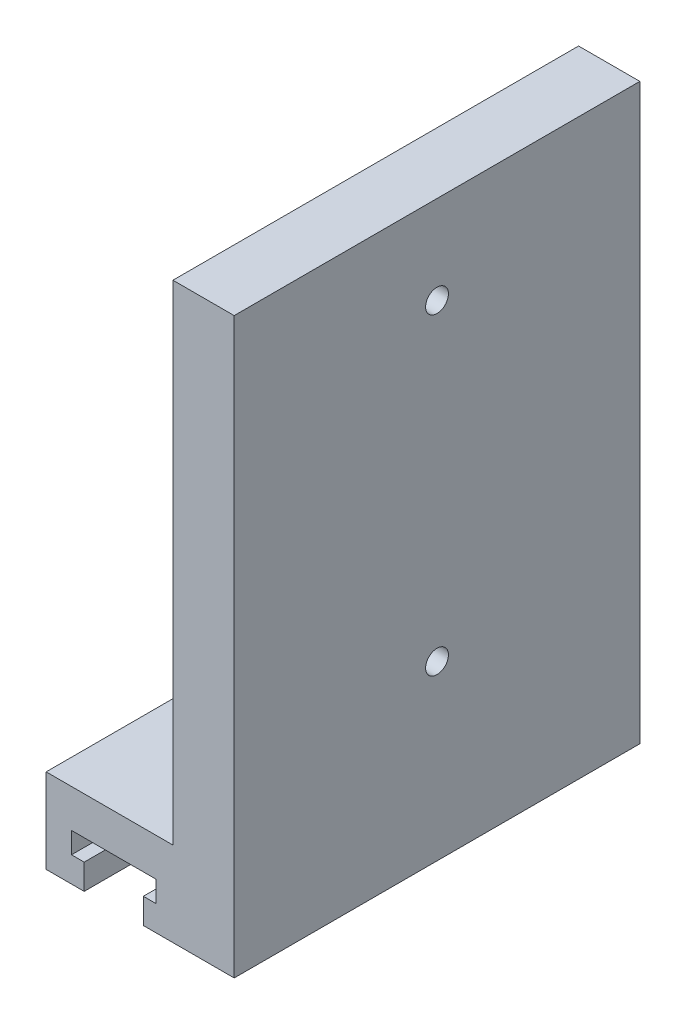
SolidWorks part; units mm, degrees
material "ABS"
ref_plane "Front Plane" through (0, 0, 0) normal (0, 0, 1) x (1, 0, 0)
ref_plane "Top Plane" through (0, 0, 0) normal (0, 1, 0) x (1, 0, 0)
ref_plane "Right Plane" through (0, 0, 0) normal (1, 0, 0) x (0, 0, -1)
ref_plane "Plane3" through (0, 0, 10) normal (0, 0, 1) x (1, 0, 0)
sketch "Sketch3" plane through (0, 0, 10) normal (0, 0, 1) x (1, 0, 0)
  line L0 (-8, 13) -> (-3.5, 13)
  line L5 (3.5, 13) -> (14.25, 13)
  line L6 (14.25, 13) -> (14.25, 80.88)
  line L7 (-8, 13) -> (-8, 23)
  line L8 (-8, 23) -> (7, 23)
  line L9 (7, 23) -> (7, 80.88)
  line L10 (7, 80.88) -> (14.25, 80.88)
  line L11 (-3.5, 13) -> (-3.5, 16)
  line L12 (-3.5, 16) -> (-5, 16)
  line L13 (-5, 16) -> (-5, 18.5)
  line L14 (-5, 18.5) -> (5, 18.5)
  line L15 (5, 18.5) -> (5, 16)
  line L16 (5, 16) -> (3.5, 16)
  line L17 (3.5, 16) -> (3.5, 13)
  dimension "D1" = 57.88
  dimension "D2" = 15
  dimension "D3" = 13
  dimension "D4" = 10
  dimension "D5" = 7.25
  dimension "D6" = 2.5
  dimension "D7" = 4.5
  dimension "D8" = 8
  dimension "D9" = 3
  dimension "D10" = 1.5
  dimension "D11" = 10
extrude "Boss-Extrude1" add sketch "Sketch3" against normal blind 48
sketch "Sketch4" plane through (7, 0, 0) normal (-1, 0, 0) x (0, 0, 1)
  line L0 (-38, 51.94) -> (10, 51.94) construction
  line L1 (-28.5, 63.94) -> (12.5, 63.94)
  line L2 (-28.5, 63.94) -> (-28.5, 39.94)
  line L3 (-28.5, 39.94) -> (12.5, 39.94)
  line L4 (12.5, 63.94) -> (12.5, 39.94)
  line L5 (-28.5, 63.94) -> (12.5, 39.94) construction
  line L6 (-28.5, 39.94) -> (12.5, 63.94) construction
  line L9 (-38, 80.88) -> (-38, 23) construction
  line L10 (10, 80.88) -> (10, 23) construction
  point P0 (-8, 51.94)
  dimension "D1" = 41
  dimension "D2" = 24
  dimension "D3" = 9.5
extrude "Cut-Extrude1" [suppressed] cut sketch "Sketch4" against normal blind 20
sketch "Sketch5" [suppressed] plane through (52, 0, 0) normal (-1, 0, 0) x (0, 0, 1)
  line L0 (-6.8, 39.94) -> (-47.8, 63.94) construction
  line L1 (-51.585, 56.995) -> (-3.015, 56.995) construction
  line L2 (-51.585, 56.995) -> (-51.585, 46.885) construction
  line L3 (-51.585, 46.885) -> (-3.015, 46.885) construction
  line L4 (-3.015, 56.995) -> (-3.015, 46.885) construction
  line L5 (-51.585, 56.995) -> (-3.015, 46.885) construction
  line L6 (-51.585, 46.885) -> (-3.015, 56.995) construction
  line L12 (-47.8, 63.94) -> (-47.8, 39.94) construction
  line L13 (-6.8, 63.94) -> (-47.8, 63.94) construction
  line L14 (-6.8, 39.94) -> (-6.8, 63.94) construction
  line L15 (-47.8, 39.94) -> (-6.8, 39.94) construction
  circle A0 centre (-51.585, 56.995) radius 2.15
  circle A1 centre (-51.585, 46.885) radius 2.15
  circle A2 centre (-3.015, 56.995) radius 2.15
  circle A3 centre (-3.015, 46.885) radius 2.15
  point P0 (-27.3, 51.94)
  dimension "D3" = 4.3
  dimension "D1" = 48.57
  dimension "D2" = 10.11
extrude "Cut-Extrude2" [suppressed] cut sketch "Sketch5" against normal blind 5.1594
hole_wizard "M2.5 Clearance Hole1" [suppressed] positions "Sketch6" profile "Sketch7" hole size "M2.5" standard "ISO"
sketch "Sketch6" plane through (0, 23, 0) normal (0, 1, 0) x (1, 0, 0)
  point P0 (0, 13.65)
sketch "Sketch7" plane through (0, 23, -13.65) normal (1, 0, 0) x (0, 0, 1)
  line L0 (0, 0) -> (0, 10)
  line L1 (0, 10) -> (1.35, 10)
  line L2 (1.35, 10) -> (1.35, 0)
  line L5 (1.35, 0) -> (0, 0)
  line L11 (0, -6.35) -> (0, 107.95) construction
  dimension "Thru Hole Dia." = 2.7
  dimension "Thru Hole Depth" = 10
hole_wizard "M2.5 Clearance Hole2" positions "Sketch8" profile "Sketch9" hole size "M2.5" standard "ISO" end condition through all
sketch "Sketch8" plane through (0, 23, 0) normal (0, 1, 0) x (1, 0, 0)
  point P0 (0, 14)
sketch "Sketch9" plane through (0, 23, -14) normal (1, 0, 0) x (0, 0, 1)
  line L0 (0, 0) -> (0, 10)
  line L1 (0, 10) -> (1.35, 10)
  line L2 (1.35, 10) -> (1.35, 0)
  line L5 (1.35, 0) -> (0, 0)
  line L11 (0, -6.35) -> (0, 107.95) construction
  dimension "Thru Hole Dia." = 2.7
  dimension "Thru Hole Depth" = 10
sketch "Sketch10" plane through (7, 0, 0) normal (-1, 0, 0) x (0, 0, 1)
  line L0 (10, 23) -> (-38, 80.88) construction
  line L1 (-38, 80.88) -> (-38, 23) construction
  line L2 (-38, 80.88) -> (10, 80.88) construction
  line L3 (-38, 23) -> (10, 23) construction
  line L4 (10, 80.88) -> (10, 23) construction
  line L5 (-14, 70.44) -> (-14, 33.44) construction
  circle A0 centre (-14, 70.44) radius 6.8186
  circle A1 centre (-14, 33.44) radius 3.5515
  point P11 (-14, 51.94)
  dimension "D1" = 37
hole_wizard "M2.5 Clearance Hole3" positions "Sketch12" profile "Sketch13" hole size "M2.5" standard "ISO" end condition through all
sketch "Sketch12" plane through (7, 0, 0) normal (-1, 0, 0) x (0, 0, 1)
  line L0 (-38, 80.88) -> (10, 23) construction
  line L1 (-38, 80.88) -> (10, 80.88) construction
  line L2 (-38, 80.88) -> (-38, 23) construction
  line L3 (10, 80.88) -> (10, 23) construction
  line L4 (-38, 23) -> (10, 23) construction
  line L5 (-14, 70.44) -> (-14, 33.44) construction
  point P0 (-14, 70.44)
  point P2 (-14, 33.44)
  point P33 (-14, 70.44)
  point P34 (-14, 33.44)
  point P35 (0, 0)
  dimension "D1" = 37
sketch "Sketch13" plane through (7, 70.44, -14) normal (0, 1, 0) x (0, 0, 1)
  line L0 (0, 0) -> (0, 7.25)
  line L1 (0, 7.25) -> (1.35, 7.25)
  line L2 (1.35, 7.25) -> (1.35, 0)
  line L5 (1.35, 0) -> (0, 0)
  line L11 (0, -6.35) -> (0, 107.95) construction
  dimension "Thru Hole Dia." = 2.7
  dimension "Thru Hole Depth" = 7.25
